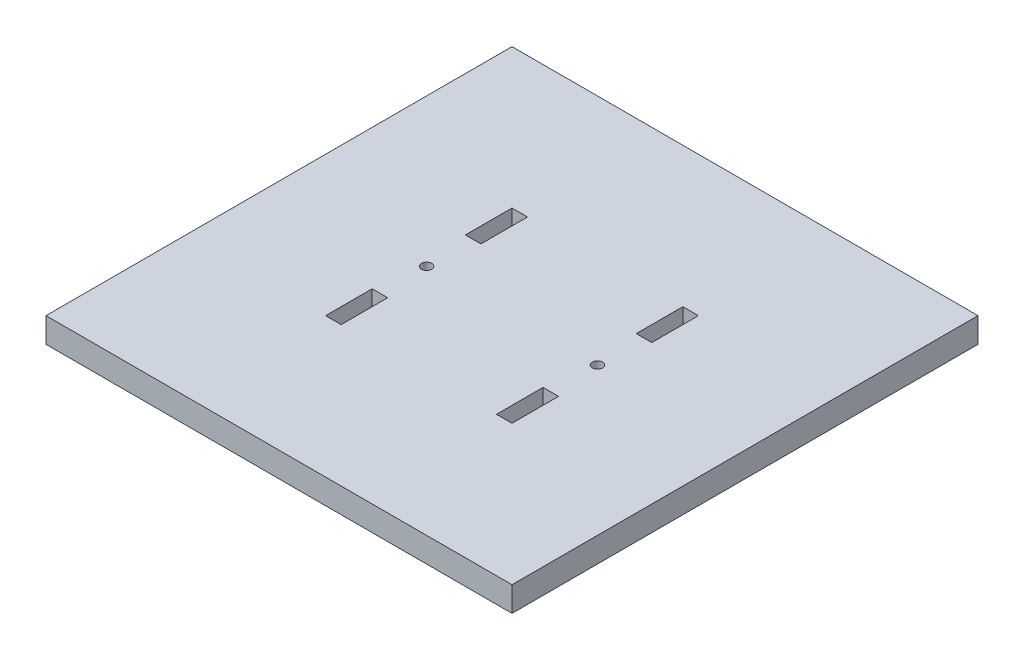
SolidWorks part; units mm, degrees
material "Acrylic (Medium-high impact)"
ref_plane "Front Plane" through (0, 0, 0) normal (0, 0, 1) x (1, 0, 0)
ref_plane "Top Plane" through (0, 0, 0) normal (0, 1, 0) x (1, 0, 0)
ref_plane "Right Plane" through (0, 0, 0) normal (1, 0, 0) x (0, 0, -1)
sketch "Sketch1" plane through (0, 0, 0) normal (0, 1, 0) x (1, 0, 0)
  line L0 (75, 150) -> (75, 0) construction
  line L1 (0, 0) -> (150, 0)
  line L2 (0, 0) -> (0, 150)
  line L3 (0, 150) -> (150, 150)
  line L4 (150, 0) -> (150, 150)
  line L5 (0, 75) -> (150, 75) construction
  line L6 (100, 45) -> (100, 60)
  line L7 (100, 105) -> (105, 105)
  line L8 (100, 105) -> (100, 90)
  line L9 (100, 90) -> (105, 90)
  line L10 (105, 105) -> (105, 90)
  line L11 (100, 60) -> (105, 60)
  line L12 (105, 45) -> (105, 60)
  line L13 (100, 45) -> (105, 45)
  line L14 (50, 45) -> (45, 45)
  line L15 (45, 45) -> (45, 60)
  line L16 (50, 60) -> (45, 60)
  line L17 (45, 105) -> (45, 90)
  line L18 (50, 90) -> (45, 90)
  line L19 (50, 105) -> (50, 90)
  line L20 (50, 105) -> (45, 105)
  line L21 (50, 45) -> (50, 60)
  circle A0 centre (102.5, 75) radius 1.65
  circle A1 centre (47.5, 75) radius 1.65
  point P29 (102.5, 90)
  dimension "D5" = 3.3
  dimension "D1" = 150
  dimension "D2" = 150
  dimension "D3" = 5
  dimension "D4" = 15
  dimension "D6" = 25
  dimension "D7" = 15
extrude "Boss-Extrude1" add sketch "Sketch1" along normal blind 8
